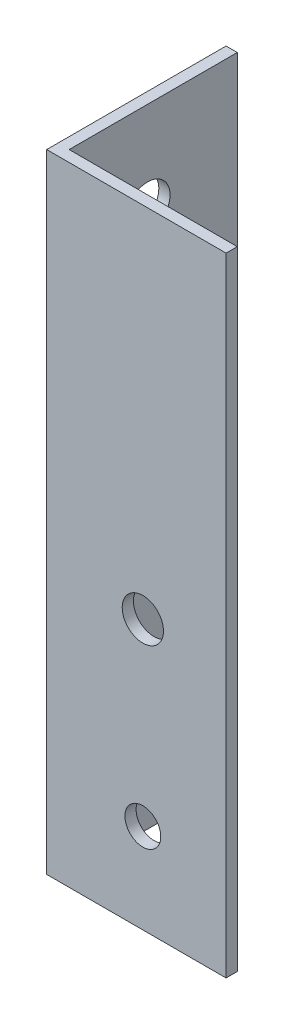
SolidWorks part; units mm, degrees
ref_plane "Front Plane" through (0, 0, 0) normal (0, 0, 1) x (1, 0, 0)
ref_plane "Top Plane" through (0, 0, 0) normal (0, 1, 0) x (1, 0, 0)
ref_plane "Right Plane" through (0, 0, 0) normal (1, 0, 0) x (0, 0, -1)
sketch "Sketch1" plane through (0, 0, 0) normal (0, 1, 0) x (1, 0, 0)
  line L0 (0, 25.4) -> (0, 0)
  line L1 (0, 0) -> (25.4, 0)
  line L2 (25.4, 0) -> (25.4, 1.5875)
  line L3 (25.4, 1.5875) -> (1.5875, 1.5875)
  line L4 (1.5875, 1.5875) -> (1.5875, 25.4)
  line L5 (1.5875, 25.4) -> (0, 25.4)
  dimension "D1" = 1.5875
  dimension "D2" = 25.4
extrude "Boss-Extrude1" add sketch "Sketch1" along normal blind 88.9
sketch "Sketch2" plane through (0, 0, -1.5875) normal (0, 0, -1) x (-1, 0, 0)
  line L1 (-25.4, 0) -> (-1.5875, 0) construction
  circle A0 centre (-13.6129, 12.7) radius 2.54
  circle A1 centre (-13.6129, 38.1) radius 2.9229
  dimension "D1" = 12.7
  dimension "D3" = 5.08
  dimension "D2" = 25.4
extrude "Cut-Extrude1" cut sketch "Sketch2" against normal blind 88.9
sketch "Sketch3" plane through (1.5875, 0, 0) normal (1, 0, 0) x (0, 0, -1)
  line L0 (1.5875, 88.9) -> (25.4, 88.9) construction
  line L1 (25.4, 88.9) -> (25.4, 0) construction
  circle A0 centre (12.7, 76.2) radius 3.175
  dimension "D1" = 12.7
  dimension "D2" = 12.7
  dimension "D3" = 6.35
extrude "Cut-Extrude2" cut sketch "Sketch3" against normal blind 88.9
